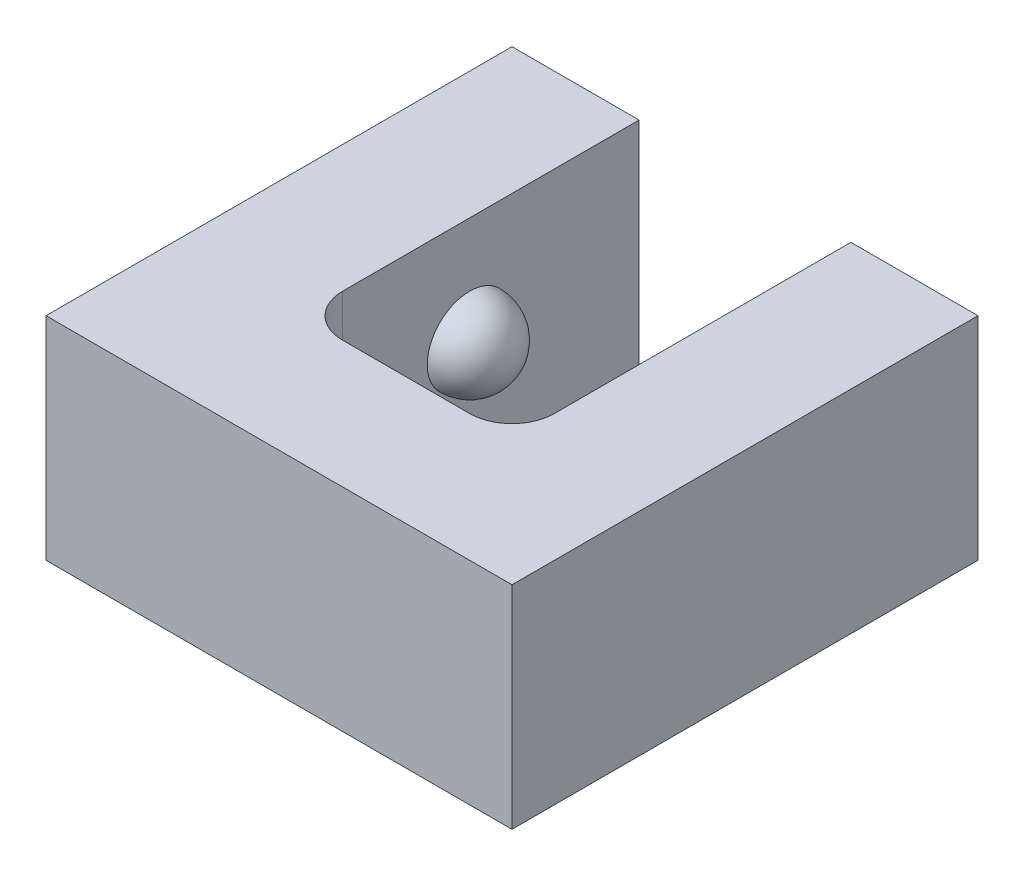
SolidWorks part; units mm, degrees
ref_plane "Front Plane" through (0, 0, 0) normal (0, 0, 1) x (1, 0, 0)
ref_plane "Top Plane" through (0, 0, 0) normal (0, 1, 0) x (1, 0, 0)
ref_plane "Right Plane" through (0, 0, 0) normal (1, 0, 0) x (0, 0, -1)
sketch "Sketch1" plane through (0, 0, 0) normal (0, 1, 0) x (1, 0, 0)
  line L0 (-5.5, -5.5) -> (-5.5, 5.5)
  line L1 (-2.5, -2.5) -> (2.5, -2.5)
  line L2 (-2.5, -2.5) -> (-2.5, 5.5)
  line L3 (-2.5, 2.5) -> (2.5, 2.5)
  line L4 (2.5, -2.5) -> (2.5, 5.5)
  line L5 (-2.5, -2.5) -> (2.5, 2.5) construction
  line L6 (-2.5, 2.5) -> (2.5, -2.5) construction
  line L7 (-5.5, 5.5) -> (5.5, 5.5)
  line L8 (5.5, -5.5) -> (5.5, 5.5)
  line L9 (-5.5, -5.5) -> (5.5, -5.5)
  line L10 (2.5, -2.5) -> (2.5, 2.5) construction
  line L11 (-2.5, -2.5) -> (-2.5, 2.5) construction
  point P0 (0, 0)
  dimension "D1" = 5
  dimension "D2" = 5
  dimension "D3" = 3
extrude "Boss-Extrude1" add sketch "Sketch1" along normal blind 5 contours L0 L9 L8 L7 L4 L1 L2
sketch "Sketch2" plane through (-2.5, 0, 0) normal (1, 0, 0) x (0, 0, -1)
  line L0 (5.5, 2.5) -> (-2.5, 2.5) construction
  line L1 (5.5, 5) -> (5.5, 0) construction
  line L2 (-2.5, 5) -> (-2.5, 0) construction
  line L3 (2.5, 2.5) -> (0.5, 2.5)
  arc A0 (0.5, 2.5) -> (2.5, 2.5) centre (1.5, 2.5) ccw
ref_plane "Plane1" through (0, 2.5, 0) normal (0, 1, 0) x (1, 0, 0)
ref_plane "Plane2" through (0, 0, 0) normal (1, 0, 0) x (0, -1, 0)
revolve "Revolve1" add sketch "Sketch2" angle 360 about L0
mirror "Mirror1" about plane through (0, 0, 0) normal (1, 0, 0) of "Revolve1"
fillet "Fillet1" radius 1 2 edges at (2.5, 2.5, 2.5) (-2.5, 2.5, 2.5)
